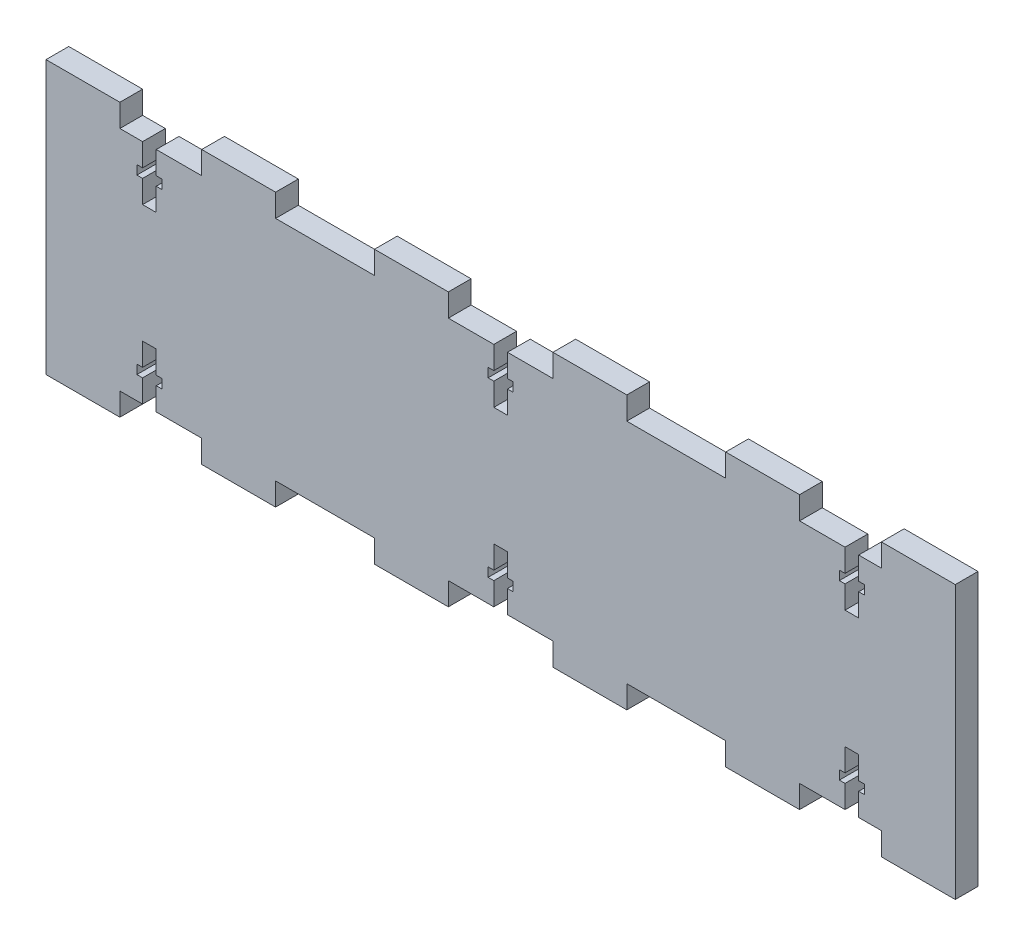
SolidWorks part; units mm, degrees
ref_plane "Front Plane" through (0, 0, 0) normal (0, 0, 1) x (1, 0, 0)
ref_plane "Top Plane" through (0, 0, 0) normal (0, 1, 0) x (1, 0, 0)
ref_plane "Right Plane" through (0, 0, 0) normal (1, 0, 0) x (0, 0, -1)
sketch "Sketch1" plane through (0, 0, 0) normal (0, 0, 1) x (1, 0, 0)
  line L1 (-100, -25) -> (100, -25)
  line L2 (-100, -25) -> (-100, 25)
  line L3 (-100, 25) -> (100, 25)
  line L4 (100, -25) -> (100, 25)
  line L5 (-100, -25) -> (100, 25) construction
  line L6 (-100, 25) -> (100, -25) construction
  point P0 (0, 0)
  dimension "D1" = 50
  dimension "D2" = 200
extrude "Boss-Extrude1" add sketch "Sketch1" along normal blind 5
sketch "Sketch2" plane through (0, 0, 5) normal (0, 0, 1) x (1, 0, 0)
  line L0 (-100, -25) -> (100, -25) construction
  line L1 (-80, -18) -> (-74.5, -18)
  line L2 (-80, -18) -> (-80, -20)
  line L3 (-80, -20) -> (-74.5, -20)
  line L4 (-74.5, -18) -> (-74.5, -20)
  line L5 (-80, -18) -> (-74.5, -20) construction
  line L6 (-80, -20) -> (-74.5, -18) construction
  line L7 (-75.75, -13) -> (-78.75, -13)
  line L8 (-75.75, -13) -> (-75.75, -25)
  line L9 (-75.75, -25) -> (-78.75, -25)
  line L10 (-78.75, -13) -> (-78.75, -25)
  line L11 (-75.75, -13) -> (-78.75, -25) construction
  line L12 (-75.75, -25) -> (-78.75, -13) construction
  line L14 (-2.75, -18) -> (2.75, -18)
  line L15 (-2.75, -18) -> (-2.75, -20)
  line L16 (-2.75, -20) -> (2.75, -20)
  line L17 (2.75, -18) -> (2.75, -20)
  line L18 (1.5, -13) -> (-1.5, -13)
  line L19 (1.5, -13) -> (1.5, -25)
  line L20 (1.5, -25) -> (-1.5, -25)
  line L21 (-1.5, -13) -> (-1.5, -25)
  line L22 (-2.75, -18) -> (2.75, -20) construction
  line L23 (-2.75, -20) -> (2.75, -18) construction
  line L24 (1.5, -13) -> (-1.5, -25) construction
  line L25 (1.5, -25) -> (-1.5, -13) construction
  line L26 (74.5, -18) -> (80, -18)
  line L27 (74.5, -18) -> (74.5, -20)
  line L28 (74.5, -20) -> (80, -20)
  line L29 (80, -18) -> (80, -20)
  line L30 (78.75, -13) -> (75.75, -13)
  line L31 (78.75, -13) -> (78.75, -25)
  line L32 (78.75, -25) -> (75.75, -25)
  line L33 (75.75, -13) -> (75.75, -25)
  line L34 (74.5, -18) -> (80, -20) construction
  line L35 (74.5, -20) -> (80, -18) construction
  line L36 (78.75, -13) -> (75.75, -25) construction
  line L37 (78.75, -25) -> (75.75, -13) construction
  line L38 (-100, 25) -> (-100, -25) construction
  point P0 (-77.25, -19)
  point P5 (-77.25, -19)
  point P16 (0, -19)
  point P21 (0, -19)
  point P26 (77.25, -19)
  point P31 (77.25, -19)
  dimension "D1" = 3
  dimension "D2" = 12
  dimension "D3" = 2
  dimension "D4" = 5.5
  dimension "D5" = 3
  dimension "D6" = 20
extrude "Cut-Extrude1" cut sketch "Sketch2" against normal blind 5 contours L1 L4 L3 L2 | L10 L9 L8 L7 | L19 L20 L21 L18 | L17 L16 L15 L14 | L31 L32 L33 L30 | L29 L28 L27 L26
sketch "Sketch3" plane through (0, 0, 5) normal (0, 0, 1) x (1, 0, 0)
  line L1 (-100, -25) -> (-83.75, -25)
  line L2 (-100, -25) -> (-100, -30)
  line L3 (-100, -30) -> (-83.75, -30)
  line L4 (-83.75, -25) -> (-83.75, -30)
  line L6 (-27.75, -25) -> (-11.5, -25)
  line L7 (-27.75, -25) -> (-27.75, -30)
  line L8 (-27.75, -30) -> (-11.5, -30)
  line L9 (-11.5, -25) -> (-11.5, -30)
  line L11 (11.5, -25) -> (27.75, -25)
  line L12 (11.5, -25) -> (11.5, -30)
  line L13 (11.5, -30) -> (27.75, -30)
  line L14 (27.75, -25) -> (27.75, -30)
  line L16 (49.5, -25) -> (65.75, -25)
  line L17 (49.5, -25) -> (49.5, -30)
  line L18 (49.5, -30) -> (65.75, -30)
  line L19 (65.75, -25) -> (65.75, -30)
  line L21 (83.75, -25) -> (100, -25)
  line L22 (83.75, -25) -> (83.75, -30)
  line L23 (83.75, -30) -> (100, -30)
  line L24 (100, -25) -> (100, -30)
  line L25 (100, -25) -> (100, 25) construction
  line L27 (1.5, -20) -> (1.5, -25) construction
  line L28 (-78.75, -13) -> (-78.75, -18) construction
  line L29 (-75.75, -20) -> (-75.75, -25) construction
  line L31 (-65.75, -25) -> (-49.5, -25)
  line L32 (-65.75, -25) -> (-65.75, -30)
  line L33 (-65.75, -30) -> (-49.5, -30)
  line L34 (-49.5, -25) -> (-49.5, -30)
  line L35 (-31.5, -25) -> (-15.25, -25) [skipped]
  line L36 (-31.5, -25) -> (-31.5, -30) [skipped]
  line L37 (-31.5, -30) -> (-15.25, -30) [skipped]
  line L38 (-15.25, -25) -> (-15.25, -30) [skipped]
  line L39 (2.75, -25) -> (19, -25) [skipped]
  line L40 (2.75, -25) -> (2.75, -30) [skipped]
  line L41 (2.75, -30) -> (19, -30) [skipped]
  line L42 (19, -25) -> (19, -30) [skipped]
  line L43 (37, -25) -> (53.25, -25) [skipped]
  line L44 (37, -25) -> (37, -30) [skipped]
  line L45 (37, -30) -> (53.25, -30) [skipped]
  line L46 (53.25, -25) -> (53.25, -30) [skipped]
  line L47 (71.25, -25) -> (87.5, -25) [skipped]
  line L48 (71.25, -25) -> (71.25, -30) [skipped]
  line L49 (71.25, -30) -> (87.5, -30) [skipped]
  line L50 (87.5, -25) -> (87.5, -30) [skipped]
  line L51 (105.5, -25) -> (121.75, -25) [skipped]
  line L52 (105.5, -25) -> (105.5, -30) [skipped]
  line L53 (105.5, -30) -> (121.75, -30) [skipped]
  line L54 (121.75, -25) -> (121.75, -30) [skipped]
  line L55 (-1.5, -20) -> (-1.5, -25) construction
  line L56 (75.75, -20) -> (75.75, -25) construction
  point P5 (1.5, -22.5)
  point P7 (-78.75, -15.5)
  point P15 (75.75, -22.5)
  dimension "D2" = 5
  dimension "D4" = 2
  dimension "D5" = 10
  dimension "D7" = 10
  dimension "D9" = 10
  dimension "D11" = 10
  dimension "D12" = 5
  dimension "D3" = 2
  dimension "D6" = 2
  dimension "D8" = 2
  dimension "D10" = 2
extrude "Boss-Extrude2" add sketch "Sketch3" against normal blind 5
mirror "Mirror1" about plane through (0, 0, 0) normal (0, 1, 0) of "Cut-Extrude1", "Boss-Extrude2"
